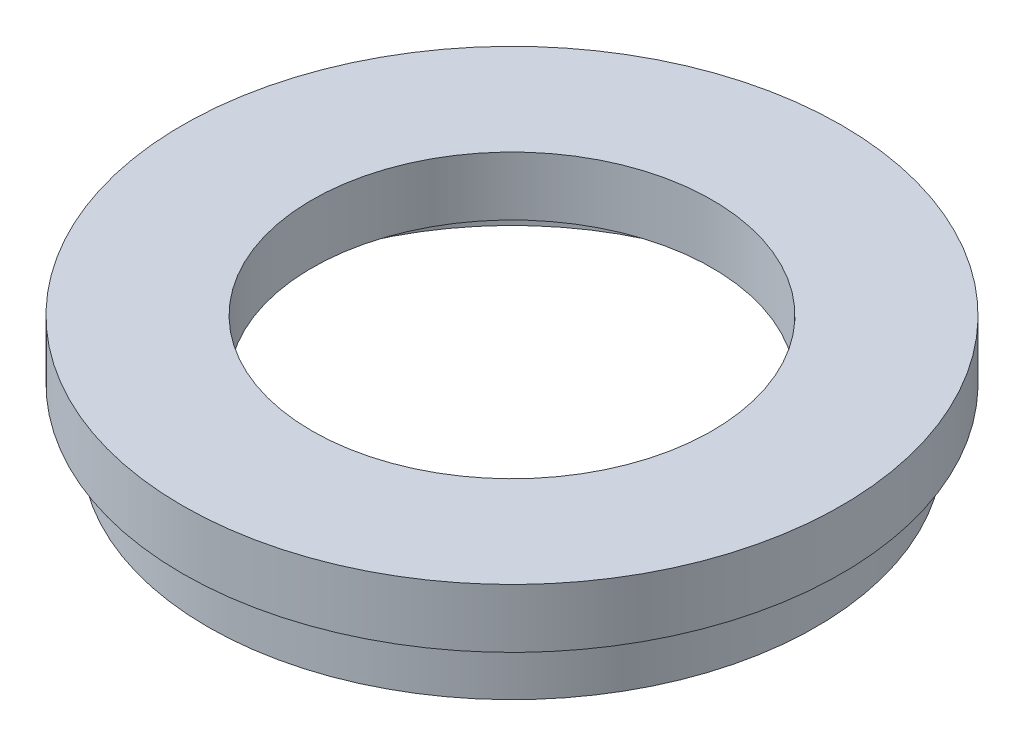
SolidWorks part; units mm, degrees
ref_plane "前视基准面" through (0, 0, 0) normal (0, 0, 1) x (1, 0, 0)
ref_plane "上视基准面" through (0, 0, 0) normal (0, 1, 0) x (1, 0, 0)
ref_plane "右视基准面" through (0, 0, 0) normal (1, 0, 0) x (0, 0, -1)
sketch "草图1" plane through (0, 0, 0) normal (0, 0, 1) x (1, 0, 0)
  line L0 (0, 13.7447) -> (0, -18.6809) construction
  line L1 (25.845, 0) -> (23.5, 0)
  line L2 (23.5, 0) -> (23.5, 4)
  line L3 (23.5, 4) -> (24.1, 4)
  line L4 (24.1, 4) -> (24.1, 5)
  line L5 (24.1, 5) -> (17, 5)
  line L6 (17, 5) -> (17, 10)
  line L7 (17, 10) -> (28, 10)
  line L8 (28, 10) -> (28, 5)
  line L9 (28, 5) -> (25.45, 5)
  line L10 (25.45, 5) -> (25.45, 4)
  line L11 (25.45, 4) -> (25.845, 4)
  line L12 (25.845, 4) -> (25.845, 0)
  point P5 (20.8085, 0)
  dimension "D1" = 10
  dimension "D2" = 28
  dimension "D3" = 17
  dimension "D4" = 23.5
  dimension "D5" = 24.1
  dimension "D6" = 25.845
  dimension "D7" = 25.45
  dimension "D8" = 1
  dimension "D9" = 1
  dimension "D10" = 5
  dimension "D11" = 5
revolve "旋转1" add sketch "草图1" angle 360 about L0
cosmetic thread "装饰螺纹线1" parameters "D1"=5, "D2"=35
cosmetic thread "装饰螺纹线2" parameters "D1"=5, "D2"=48
cosmetic thread "装饰螺纹线3" parameters "D1"=4, "D2"=50.69
